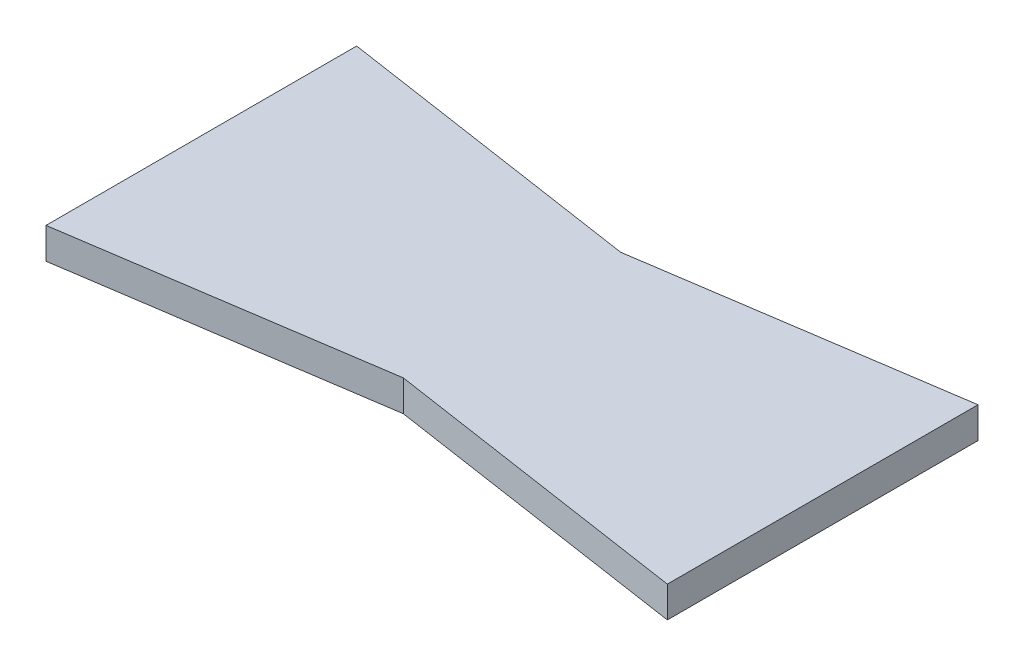
SolidWorks part; units mm, degrees
ref_plane "Front Plane" through (0, 0, 0) normal (0, 0, 1) x (1, 0, 0)
ref_plane "Top Plane" through (0, 0, 0) normal (0, 1, 0) x (1, 0, 0)
ref_plane "Right Plane" through (0, 0, 0) normal (1, 0, 0) x (0, 0, -1)
sketch "Sketch1" plane through (0, 0, 0) normal (0, 1, 0) x (1, 0, 0)
  line L0 (-33.9927, 22.1245) -> (6.0073, 16.1245)
  line L5 (6.0073, 16.1245) -> (46.0073, 22.1245)
  line L6 (-33.9927, -17.8755) -> (6.0073, -11.8755)
  line L7 (6.0073, -11.8755) -> (46.0073, -17.8755)
  line L8 (-33.9927, 22.1245) -> (-33.9927, -17.8755)
  line L9 (46.0073, 22.1245) -> (46.0073, -17.8755)
  dimension "D1" = 80
  dimension "D2" = 40
extrude "Boss-Extrude1" add sketch "Sketch1" along normal blind 4
